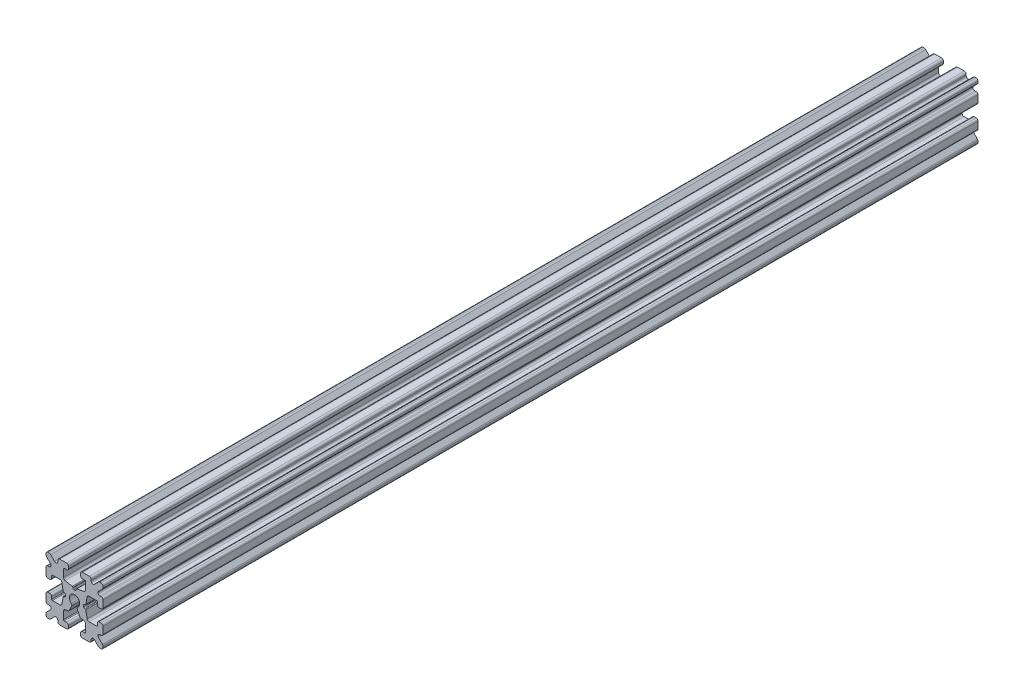
SolidWorks part; units mm, degrees
ref_plane "Front Plane" through (0, 0, 0) normal (0, 0, 1) x (1, 0, 0)
ref_plane "Top Plane" through (0, 0, 0) normal (0, 1, 0) x (1, 0, 0)
ref_plane "Right Plane" through (0, 0, 0) normal (1, 0, 0) x (0, 0, -1)
sketch "Sketch1" plane through (0, 0, 0) normal (0, 0, 1) x (1, 0, 0)
  line L1 (-7.5, -7.5) -> (7.5, -7.5)
  line L2 (-7.5, -7.5) -> (-7.5, 7.5)
  line L3 (-7.5, 7.5) -> (7.5, 7.5)
  line L4 (7.5, -7.5) -> (7.5, 7.5)
  line L5 (-7.5, -7.5) -> (7.5, 7.5) construction
  line L6 (-7.5, 7.5) -> (7.5, -7.5) construction
  circle A0 centre (0, 0) radius 1.35
  point P0 (0, 0)
  dimension "D2" = 2.7
  dimension "D1" = 15
extrude "Boss-Extrude1" add sketch "Sketch1" along normal mid plane 230.2
fillet "Fillet1" radius 0.5 4 edges at (7.5, -7.5, 0) (-7.5, -7.5, 0) (7.5, 7.5, 0) (-7.5, 7.5, 0)
sketch "Sketch2" plane through (0, 0, 115.1) normal (0, 0, 1) x (1, 0, 0)
  line L0 (-7.5, 7) -> (-7.5, -7) construction
  line L1 (-7.5, 1.6) -> (-6, 1.6)
  line L2 (-7.5, 1.6) -> (-7.5, -1.6)
  line L3 (-7.5, -1.6) -> (-6, -1.6)
  line L4 (-6, 1.6) -> (-6, 2.9)
  line L5 (0, 0) -> (-12.1036, 0) construction
  line L6 (-6, -2.9) -> (-3.4, -2.9)
  line L7 (0, 0) -> (-7, 7) construction
  line L8 (-6, 2.9) -> (-3.4, 2.9)
  line L9 (-3.4, -2.9) -> (-3.4, 2.9)
  line L10 (55, 0) -> (-55, 0) construction
  line L11 (-6, -2.9) -> (-6, -1.6)
  line L12 (2.9, 6) -> (1.6, 6)
  line L13 (2.9, 3.4) -> (-2.9, 3.4)
  line L14 (-2.9, 6) -> (-2.9, 3.4)
  line L15 (2.9, 6) -> (2.9, 3.4)
  line L16 (-1.6, 6) -> (-2.9, 6)
  line L17 (1.6, 7.5) -> (1.6, 6)
  line L18 (-1.6, 7.5) -> (1.6, 7.5)
  line L19 (-1.6, 7.5) -> (-1.6, 6)
  line L20 (-1.6, -7.5) -> (-1.6, -6)
  line L21 (-1.6, -7.5) -> (1.6, -7.5)
  line L22 (1.6, -7.5) -> (1.6, -6)
  line L23 (-1.6, -6) -> (-2.9, -6)
  line L24 (2.9, -6) -> (2.9, -3.4)
  line L25 (-2.9, -6) -> (-2.9, -3.4)
  line L26 (2.9, -3.4) -> (-2.9, -3.4)
  line L27 (2.9, -6) -> (1.6, -6)
  line L28 (6, -2.9) -> (6, -1.6)
  line L29 (3.4, -2.9) -> (3.4, 2.9)
  line L30 (6, 2.9) -> (3.4, 2.9)
  line L31 (6, -2.9) -> (3.4, -2.9)
  line L32 (6, 1.6) -> (6, 2.9)
  line L33 (7.5, -1.6) -> (6, -1.6)
  line L34 (7.5, 1.6) -> (7.5, -1.6)
  line L35 (7.5, 1.6) -> (6, 1.6)
  dimension "D1" = 3.2
  dimension "D2" = 5.8
  dimension "D3" = 1.5
  dimension "D4" = 2.6
extrude "Cut-Extrude1" cut sketch "Sketch2" against normal through all
sketch "Sketch4" plane through (0, 0, 115.1) normal (0, 0, 1) x (1, 0, 0)
  line L0 (-3.4, 2.9) -> (-2.85, 0)
  line L1 (55, 0) -> (-55, 0) construction
  line L2 (-2.85, 0) -> (-3.4, -2.9)
  line L3 (-3.4, -2.9) -> (-3.4, 2.9) construction
  line L4 (-3.4, 2.9) -> (-3.4, -2.9)
  line L5 (-2.9, 3.4) -> (0, 2.85)
  line L6 (0, 2.85) -> (2.9, 3.4)
  line L7 (2.9, 3.4) -> (-2.9, 3.4)
  line L8 (3.4, 2.9) -> (2.85, 0)
  line L9 (2.85, 0) -> (3.4, -2.9)
  line L10 (3.4, -2.9) -> (3.4, 2.9)
  line L11 (-2.9, -3.4) -> (0, -2.85)
  line L12 (0, -2.85) -> (2.9, -3.4)
  line L13 (2.9, -3.4) -> (-2.9, -3.4)
  circle A2 centre (0, 0) radius 2.85
  circle A3 centre (0, 0) radius 2.85 construction
  dimension "D1" = 1.5
extrude "Cut-Extrude3" cut sketch "Sketch4" against normal through all
fillet "Fillet3" radius 0.5 16 edges at (-6, -1.6, 0) (-7.5, -1.6, 0) (-6, 1.6, 0) (-7.5, 1.6, 0) (-1.6, -7.5, 0) (-1.6, -6, 0) (1.6, -7.5, 0) (1.6, -6, 0) (6, -1.6, 0) (7.5, -1.6, 0) (7.5, 1.6, 0) (6, 1.6, 0) (1.6, 7.5, 0) (1.6, 6, 0) (-1.6, 7.5, 0) (-1.6, 6, 0)
fillet "Fillet4" radius 0.5 8 edges at (-3.4, 2.9, 0) (-3.4, -2.9, 0) (2.9, -3.4, 0) (-2.9, -3.4, 0) (3.4, -2.9, 0) (3.4, 2.9, 0) (-2.9, 3.4, 0) (2.9, 3.4, 0)
fillet "Fillet5" radius 3 4 edges at (0, -2.85, 0) (2.85, 0, 0) (-2.85, 0, 0) (0, 2.85, 0)
fillet "Fillet6" radius 0.2 8 edges at (-2.9, -6, 0) (2.9, -6, 0) (6, -2.9, 0) (6, 2.9, 0) (2.9, 6, 0) (-2.9, 6, 0) (-6, -2.9, 0) (-6, 2.9, 0)
sketch "Sketch5" plane through (0, 0, 115.1) normal (0, 0, 1) x (1, 0, 0)
  line L0 (0, 0) -> (-7, 7) construction
  line L1 (-7.5, 6.4393) -> (-5.4607, 4.4)
  line L2 (-6.4393, 7.5) -> (-4.4, 5.4607)
  line L3 (-7.5, 4.4) -> (-5.4607, 4.4)
  line L4 (-3.8141, 2.9) -> (-5.8, 2.9) construction
  line L5 (0, 0) -> (-12.1819, 0) construction
  line L6 (-4.4, 7.5) -> (-4.4, 5.4607)
  line L7 (-2.9, 5.8) -> (-2.9, 3.8141) construction
  line L8 (-7.5, 6.4393) -> (-7.5, 4.4)
  line L9 (-7.5, 7) -> (-7.5, 2.1) construction
  line L10 (2.1, -7.5) -> (7, -7.5) construction
  line L11 (7.5, -7) -> (7.5, -2.1) construction
  line L12 (7, 7.5) -> (2.1, 7.5) construction
  line L13 (-2.1, 7.5) -> (-7, 7.5) construction
  line L14 (-4.4, 7.5) -> (-6.4393, 7.5)
  line L16 (55, 0) -> (-55, 0) construction
  line L17 (0, 0) -> (0, 10.993) construction
  line L18 (0, -54.6431) -> (0, 54.6431) construction
  line L20 (4.4, 7.5) -> (6.4393, 7.5)
  line L22 (7.5, 6.4393) -> (7.5, 4.4)
  line L23 (4.4, 7.5) -> (4.4, 5.4607)
  line L24 (7.5, 4.4) -> (5.4607, 4.4)
  line L25 (6.4393, 7.5) -> (4.4, 5.4607)
  line L26 (7.5, 6.4393) -> (5.4607, 4.4)
  line L27 (7.5, -6.4393) -> (5.4607, -4.4)
  line L28 (6.4393, -7.5) -> (4.4, -5.4607)
  line L29 (7.5, -4.4) -> (5.4607, -4.4)
  line L30 (4.4, -7.5) -> (4.4, -5.4607)
  line L31 (7.5, -6.4393) -> (7.5, -4.4)
  line L33 (4.4, -7.5) -> (6.4393, -7.5)
  line L36 (-4.4, -7.5) -> (-6.4393, -7.5)
  line L38 (-7.5, -6.4393) -> (-7.5, -4.4)
  line L39 (-4.4, -7.5) -> (-4.4, -5.4607)
  line L40 (-7.5, -4.4) -> (-5.4607, -4.4)
  line L41 (-6.4393, -7.5) -> (-4.4, -5.4607)
  line L42 (-7.5, -6.4393) -> (-5.4607, -4.4)
  dimension "D1" = 1.5
  dimension "D2" = 1.5
  dimension "D3" = 1.5
extrude "Cut-Extrude4" cut sketch "Sketch5" against normal through all
fillet "Fillet8" radius 0.5 24 edges at (-5.4607, 4.4, 0) (-7.5, 4.4, 0) (-5.4607, -4.4, 0) (-7.5, -4.4, 0) (-4.4, -7.5, 0) (-4.4, -5.4607, 0) (4.4, -7.5, 0) (4.4, -5.4607, 0) (5.4607, -4.4, 0) (7.5, -4.4, 0) (7.5, 4.4, 0) (5.4607, 4.4, 0) (4.4, 5.4607, 0) (4.4, 7.5, 0) (-4.4, 5.4607, 0) (-4.4, 7.5, 0) (-6.4393, 7.5, 0) (-7.5, 6.4393, 0) (6.4393, 7.5, 0) (7.5, 6.4393, 0) (6.4393, -7.5, 0) (7.5, -6.4393, 0) (-6.4393, -7.5, 0) (-7.5, -6.4393, 0)
sketch "Sketch6" plane through (0, 0, 115.1) normal (0, 0, 1) x (1, 0, 0)
  line L0 (0, 0) -> (0, 11.013) construction
  line L1 (0.559, 2.956) -> (2.1235, 2.956) construction
  line L2 (0, -54.6431) -> (0, 54.6431) construction
  line L3 (0, 0) -> (7, 7) construction
  line L4 (8.6552, 0.4445) -> (8.6552, -0.4445)
  line L5 (2.406, 0.4445) -> (8.6552, 0.4445)
  line L8 (2.406, -0.4445) -> (2.406, 0.4445)
  line L10 (8.6552, -0.4445) -> (2.406, -0.4445)
  line L11 (-8.6552, -0.4445) -> (-2.406, -0.4445)
  line L12 (-2.406, -0.4445) -> (-2.406, 0.4445)
  line L14 (-0.4445, 8.6552) -> (-0.4445, 2.406)
  line L15 (-0.4445, 2.406) -> (0.4445, 2.406)
  line L17 (0.4445, 2.406) -> (0.4445, 8.6552)
  line L18 (0.4445, 8.6552) -> (-0.4445, 8.6552)
  line L20 (-2.406, 0.4445) -> (-8.6552, 0.4445)
  line L21 (-8.6552, 0.4445) -> (-8.6552, -0.4445)
  point P7 (0, 2.5973)
  dimension "D3" = 0.55
  dimension "D1" = 0.889
extrude "Cut-Extrude5" cut sketch "Sketch6" against normal through all
sketch "Sketch7" plane through (0, 0, 115.1) normal (0, 0, 1) x (1, 0, 0)
  line L0 (0, 0) -> (-2.1533, -4.6178)
  line L1 (-2.1533, -4.6178) -> (2.1533, -4.6178)
  line L2 (2.1533, -4.6178) -> (0, 0)
  line L3 (0, 0) -> (0, -8.6832) construction
  line L4 (0, -54.6431) -> (0, 54.6431) construction
  dimension "D1" = 50
extrude "Cut-Extrude6" cut sketch "Sketch7" against normal through all
fillet "Fillet9" radius 0.5 4 edges at (0.5705, -1.2235, 0) (-0.5705, -1.2235, 0) (1.4579, -3.1265, 0) (-1.4579, -3.1265, 0)
fillet "Fillet10" radius 0.2 12 edges at (-2.406, 0.4445, 0) (-2.406, -0.4445, 0) (0.4445, 2.406, 0) (-0.4445, 2.406, 0) (2.406, 0.4445, 0) (2.406, -0.4445, 0) (-2.9366, -0.4445, 0) (-2.9366, 0.4445, 0) (2.9366, -0.4445, 0) (2.9366, 0.4445, 0) (0.4445, 2.9366, 0) (-0.4445, 2.9366, 0)
sketch "Sketch10" plane through (0, 0, 115.1) normal (0, 0, 1) x (1, 0, 0)
  line L0 (2.7, 6) -> (2.1, 6) construction
  line L1 (-2.75, 6) -> (2.75, 6)
  line L2 (-2.75, 6) -> (-2.75, 3.6)
  line L3 (-2.75, 3.6) -> (2.75, 3.6)
  line L4 (2.75, 6) -> (2.75, 3.6)
  line L5 (0, 0) -> (0, 8.8277) construction
  line L6 (-3.2398, 3.994) -> (-2.2083, 2.8606) construction
  line L7 (-3.878, 3.2131) -> (-3.2018, 2.4701) construction
  line L8 (-2.406, -0.2445) -> (-2.406, 0.2445) construction
  line L9 (-2.1, 7.5) -> (-3.9, 7.5) construction
  line L10 (-1.5, 7.5) -> (1.5, 7.5)
  line L11 (-1.5, 7.5) -> (-1.5, 3.5)
  line L12 (-1.5, 3.5) -> (1.5, 3.5)
  line L13 (1.5, 7.5) -> (1.5, 3.5)
  arc A1 (-3.3228, 2.4932) -> (-3.8141, 2.9) centre (-3.8141, 2.4) ccw construction
  arc A2 (-2.9, 3.8141) -> (-2.4932, 3.3228) centre (-2.4, 3.8141) ccw construction
  arc A3 (0.88, -1.0238) -> (-0.88, -1.0238) centre (0, 0) ccw construction
  point P19 (-1.35, 0)
  point P20 (-2.406, 0)
  dimension "D1" = 2.4
  dimension "D2" = 5.5
  dimension "D3" = 0.9976
  dimension "D4" = 3
  dimension "D5" = 4
sketch "Sketch11" plane through (0, 0, 115.1) normal (0, 0, 1) x (1, 0, 0)
  line L0 (-7.5, 7) -> (-7.5, 6.6464) construction
  line L1 (-7.5, 7.5) -> (7.5, 7.5) construction
  line L2 (-7.5, 7.5) -> (-7.5, -7.5) construction
  line L3 (-7.5, -7.5) -> (7.5, -7.5) construction
  line L4 (7.5, 7.5) -> (7.5, -7.5) construction
  line L5 (-7, -7.5) -> (-6.6464, -7.5) construction
  line L6 (7.5, 6.6464) -> (7.5, 7) construction
  line L7 (-2.1, 7.5) -> (-3.9, 7.5) construction
  point P0 (0, 7.5)
  point P1 (0, -7.5)
  point P2 (7.5, 0)
  point P3 (-7.5, 0)
sketch "Sketch12" plane through (0, 0, -115.1) normal (0, 0, -1) x (-1, 0, 0)
  line L1 (-7.5, -7.5) -> (7.5, -7.5) construction
  line L2 (-7.5, -7.5) -> (-7.5, 7.5) construction
  line L3 (-7.5, 7.5) -> (7.5, 7.5) construction
  line L4 (7.5, -7.5) -> (7.5, 7.5) construction
  point P4 (-7.5, 0)
  point P9 (0, -7.5)
  point P10 (7.5, 0)
  point P11 (0, 7.5)
sketch "Sketch13" plane through (0, -7.5, 0) normal (0, -1, 0) x (1, 0, 0)
  line L0 (0, 115.1) -> (0, -115.1) construction
  line L1 (-7.5, -115.1) -> (-7.5, 115.1) construction
  line L2 (7.5, 115.1) -> (7.5, -115.1) construction
sketch "Sketch14" plane through (-7.5, 0, 0) normal (-1, 0, 0) x (0, 0, 1)
  line L0 (115.1, 0) -> (-115.1, 0) construction
sketch "Sketch15" plane through (0, 7.5, 0) normal (0, 1, 0) x (1, 0, 0)
  line L0 (0, -115.1) -> (0, 115.1) construction
  line L1 (-7.5, -115.1) -> (7.5, -115.1) construction
  line L2 (-7.5, -115.1) -> (-7.5, 115.1) construction
  line L3 (7.5, 115.1) -> (7.5, -115.1) construction
sketch "Sketch16" plane through (7.5, 0, 0) normal (1, 0, 0) x (0, 0, -1)
  line L0 (-115.1, 0) -> (115.1, 0) construction
